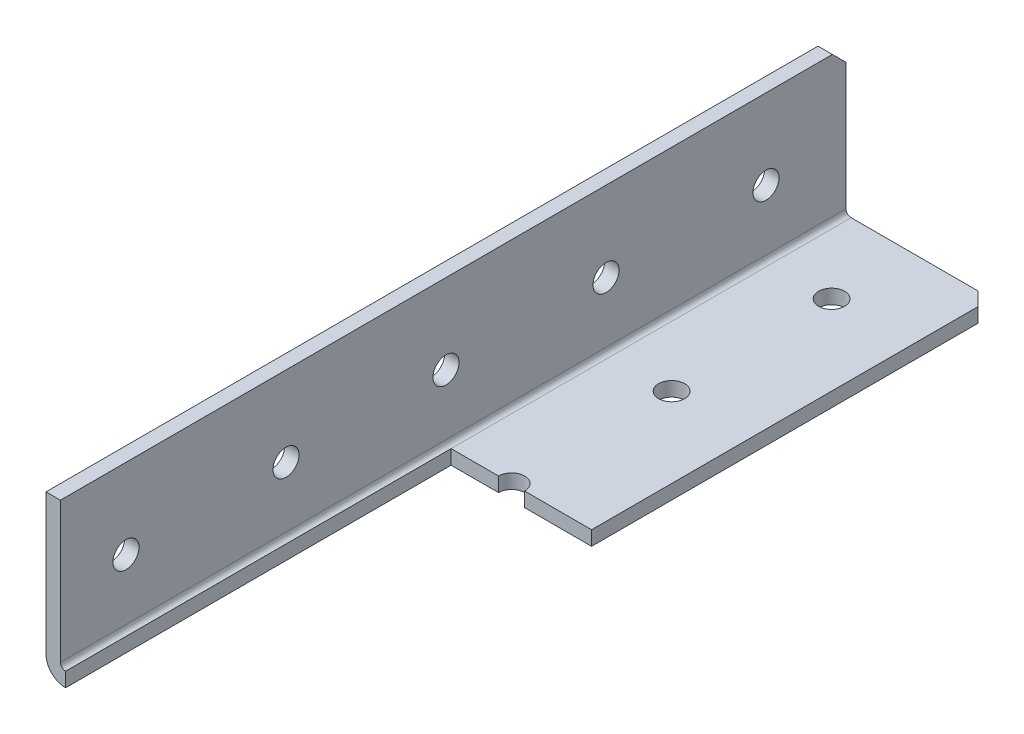
SolidWorks part; units mm, degrees
material "6061-T6 (SS)"
ref_plane "Front Plane" through (0, 0, 0) normal (0, 0, 1) x (1, 0, 0)
ref_plane "Top Plane" through (0, 0, 0) normal (0, 1, 0) x (1, 0, 0)
ref_plane "Right Plane" through (0, 0, 0) normal (1, 0, 0) x (0, 0, -1)
ref_plane "Plane1" through (0, 0, 0) normal (-1, 0, 0) x (0, -1, 0)
sketch "Sketch1" plane through (0, 0, 0) normal (-1, 0, 0) x (0, -1, 0)
  line L0 (0, 749.3) -> (-25.4, 749.3)
  line L1 (-25.4, 749.3) -> (-25.4, -749.3)
  line L2 (-25.4, -749.3) -> (0, -749.3)
  line L3 (0, -749.3) -> (0, 749.3)
extrude "Boss-Extrude1" add sketch "Sketch1" against normal blind 25.4
sketch "Sketch2" plane through (0, 0, -749.3) normal (0, 0, -1) x (-1, 0, 0)
  line L0 (-25.4, 2.286) -> (-2.286, 2.286)
  line L1 (-2.286, 2.286) -> (-2.286, 25.4)
  line L2 (-2.286, 25.4) -> (-25.4, 25.4)
  line L3 (-25.4, 25.4) -> (-25.4, 2.286)
extrude "Cut-Extrude1" cut sketch "Sketch2" against normal through all
hole_wizard "M3.5 Clearance Hole1" positions "Sketch4" profile "Sketch3" hole size "M3.5" standard "ANSI Metric"
sketch "Sketch4" plane through (0, 0, 0) normal (0, -1, 0) x (-1, 0, 0)
  point P0 (-12.7, 736.6)
  point P1 (-12.7, 711.2)
  point P2 (-12.7, 685.8)
  point P3 (-12.7, 660.4)
  point P4 (-12.7, 635)
  point P5 (-12.7, 609.6)
  point P6 (-12.7, 584.2)
  point P7 (-12.7, 558.8)
  point P8 (-12.7, 533.4)
  point P9 (-12.7, 508)
  point P10 (-12.7, 482.6)
  point P11 (-12.7, 457.2)
  point P12 (-12.7, 431.8)
  point P13 (-12.7, 406.4)
  point P14 (-12.7, 381)
  point P15 (-12.7, 355.6)
  point P16 (-12.7, 330.2)
  point P17 (-12.7, 304.8)
  point P18 (-12.7, 279.4)
  point P19 (-12.7, 254)
  point P20 (-12.7, 228.6)
  point P21 (-12.7, 203.2)
  point P22 (-12.7, 177.8)
  point P23 (-12.7, 152.4)
  point P24 (-12.7, 127)
  point P25 (-12.7, 101.6)
  point P26 (-12.7, 76.2)
  point P27 (-12.7, 50.8)
  point P28 (-12.7, 25.4)
  point P29 (-12.7, 0)
  point P30 (-12.7, -25.4)
  point P31 (-12.7, -50.8)
  point P32 (-12.7, -76.2)
  point P33 (-12.7, -101.6)
  point P34 (-12.7, -127)
  point P35 (-12.7, -152.4)
  point P36 (-12.7, -177.8)
  point P37 (-12.7, -203.2)
  point P38 (-12.7, -228.6)
  point P39 (-12.7, -254)
  point P40 (-12.7, -279.4)
  point P41 (-12.7, -304.8)
  point P42 (-12.7, -330.2)
  point P43 (-12.7, -355.6)
  point P44 (-12.7, -381)
  point P45 (-12.7, -406.4)
  point P46 (-12.7, -431.8)
  point P47 (-12.7, -457.2)
  point P48 (-12.7, -482.6)
  point P49 (-12.7, -508)
  point P50 (-12.7, -533.4)
  point P51 (-12.7, -558.8)
  point P52 (-12.7, -584.2)
  point P53 (-12.7, -609.6)
  point P54 (-12.7, -635)
  point P55 (-12.7, -660.4)
  point P56 (-12.7, -685.8)
  point P57 (-12.7, -711.2)
  point P58 (-12.7, -736.6)
sketch "Sketch3" plane through (12.7, 0, -736.6) normal (1, 0, 0) x (0, 0, -1)
  line L0 (0, 0) -> (0, 25.4)
  line L1 (0, 25.4) -> (2.0701, 25.4)
  line L2 (2.0701, 25.4) -> (2.0701, 0)
  line L5 (2.0701, 0) -> (0, 0)
  line L11 (0, -6.35) -> (0, 107.95) construction
  dimension "Thru Hole Dia." = 4.1402
  dimension "Thru Hole Depth" = 25.4
hole_wizard "M3.5 Clearance Hole2" positions "Sketch6" profile "Sketch5" hole size "M3.5" standard "ANSI Metric"
sketch "Sketch6" plane through (0, 0, 0) normal (-1, 0, 0) x (0, 0, 1)
  point P0 (711.2, 12.7)
  point P1 (736.6, 12.7)
  point P2 (685.8, 12.7)
  point P3 (660.4, 12.7)
  point P4 (635, 12.7)
  point P5 (609.6, 12.7)
  point P6 (584.2, 12.7)
  point P7 (558.8, 12.7)
  point P8 (533.4, 12.7)
  point P9 (508, 12.7)
  point P10 (482.6, 12.7)
  point P11 (457.2, 12.7)
  point P12 (431.8, 12.7)
  point P13 (406.4, 12.7)
  point P14 (381, 12.7)
  point P15 (355.6, 12.7)
  point P16 (330.2, 12.7)
  point P17 (304.8, 12.7)
  point P18 (279.4, 12.7)
  point P19 (254, 12.7)
  point P20 (228.6, 12.7)
  point P21 (203.2, 12.7)
  point P22 (177.8, 12.7)
  point P23 (152.4, 12.7)
  point P24 (127, 12.7)
  point P25 (101.6, 12.7)
  point P26 (76.2, 12.7)
  point P27 (50.8, 12.7)
  point P28 (25.4, 12.7)
  point P29 (0, 12.7)
  point P30 (-25.4, 12.7)
  point P31 (-50.8, 12.7)
  point P32 (-76.2, 12.7)
  point P33 (-101.6, 12.7)
  point P34 (-127, 12.7)
  point P35 (-152.4, 12.7)
  point P36 (-177.8, 12.7)
  point P37 (-203.2, 12.7)
  point P38 (-228.6, 12.7)
  point P39 (-254, 12.7)
  point P40 (-279.4, 12.7)
  point P41 (-304.8, 12.7)
  point P42 (-330.2, 12.7)
  point P43 (-355.6, 12.7)
  point P44 (-381, 12.7)
  point P45 (-406.4, 12.7)
  point P46 (-431.8, 12.7)
  point P47 (-457.2, 12.7)
  point P48 (-482.6, 12.7)
  point P49 (-508, 12.7)
  point P50 (-533.4, 12.7)
  point P51 (-558.8, 12.7)
  point P52 (-584.2, 12.7)
  point P53 (-609.6, 12.7)
  point P54 (-635, 12.7)
  point P55 (-660.4, 12.7)
  point P56 (-685.8, 12.7)
  point P57 (-711.2, 12.7)
  point P58 (-736.6, 12.7)
sketch "Sketch5" plane through (0, 12.7, 711.2) normal (0, 1, 0) x (0, 0, 1)
  line L0 (0, 0) -> (0, 25.4)
  line L1 (0, 25.4) -> (2.0701, 25.4)
  line L2 (2.0701, 25.4) -> (2.0701, 0)
  line L5 (2.0701, 0) -> (0, 0)
  line L11 (0, -6.35) -> (0, 107.95) construction
  dimension "Thru Hole Dia." = 4.1402
  dimension "Thru Hole Depth" = 25.4
chamfer "Chamfer1" distance 2.159 angle 45 4 edges at (25.4, 1.143, -749.3) (1.143, 25.4, -749.3) (1.143, 25.4, 749.3) (25.4, 1.143, 749.3)
fillet "Fillet1" radius 0.8128 1 edges at (2.286, 2.286, 0)
fillet "Fillet2" radius 3.0988 1 edges at (0, 0, 0)
sketch "Sketch8" plane through (0, 0, 749.3) normal (0, 0, 1) x (1, 0, 0)
  line L1 (-45.6555, -36.5704) -> (50.2275, -36.5704)
  line L2 (-45.6555, -36.5704) -> (-45.6555, 42.768)
  line L3 (-45.6555, 42.768) -> (50.2275, 42.768)
  line L4 (50.2275, -36.5704) -> (50.2275, 42.768)
  line L5 (-45.6555, -36.5704) -> (50.2275, 42.768) construction
  line L6 (-45.6555, 42.768) -> (50.2275, -36.5704) construction
  point P0 (2.286, 3.0988)
extrude "Cut-Extrude3" cut sketch "Sketch8" against normal blind 1371.6
sketch "Sketch11" plane through (0, 0, -622.3) normal (0, 0, 1) x (1, 0, 0)
  line L1 (-23.8761, -31.5895) -> (27.5864, -31.5895)
  line L2 (-23.8761, -31.5895) -> (-23.8761, 35.0872)
  line L3 (-23.8761, 35.0872) -> (27.5864, 35.0872)
  line L4 (27.5864, -31.5895) -> (27.5864, 35.0872)
  line L5 (-23.8761, -31.5895) -> (27.5864, 35.0872) construction
  line L6 (-23.8761, 35.0872) -> (27.5864, -31.5895) construction
  point P0 (1.8552, 1.7488)
extrude "Cut-Extrude6" cut sketch "Sketch11" against normal blind 2.286
sketch "Sketch12" plane through (0, 2.286, 0) normal (0, 1, 0) x (1, 0, 0)
  line L0 (3.0988, 749.3) -> (3.0988, 624.586) construction
  line L1 (3.0988, 685.8) -> (25.4, 685.8)
  line L2 (3.0988, 685.8) -> (3.0988, 624.586)
  line L3 (3.0988, 624.586) -> (25.4, 624.586)
  line L4 (25.4, 685.8) -> (25.4, 624.586)
extrude "Cut-Extrude7" cut sketch "Sketch12" against normal blind 2.54
